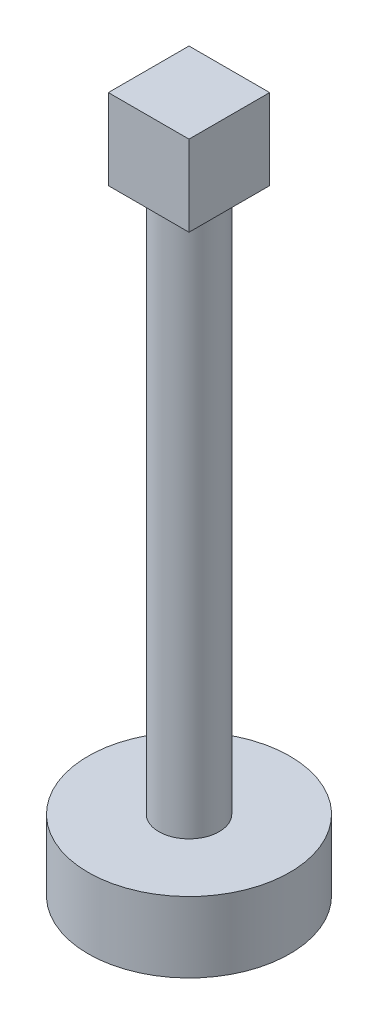
SolidWorks part; units mm, degrees
material "AISI 347 Annealed Stainless Steel (SS)"
ref_plane "Front Plane" through (0, 0, 0) normal (0, 0, 1) x (1, 0, 0)
ref_plane "Top Plane" through (0, 0, 0) normal (0, 1, 0) x (1, 0, 0)
ref_plane "Right Plane" through (0, 0, 0) normal (1, 0, 0) x (0, 0, -1)
sketch "Sketch1" plane through (0, 0, 0) normal (0, 1, 0) x (1, 0, 0)
  circle A0 centre (0, 0) radius 50
  dimension "D1" = 100
extrude "Boss-Extrude1" add sketch "Sketch1" along normal blind 35
sketch "Sketch2" plane through (0, 35, 0) normal (0, 1, 0) x (1, 0, 0)
  circle A0 centre (0, 0) radius 15
extrude "Boss-Extrude2" add sketch "Sketch2" along normal blind 270
sketch "Sketch3" plane through (0, 305, 0) normal (0, 1, 0) x (1, 0, 0)
  line L1 (-20, -20) -> (20, -20)
  line L2 (-20, -20) -> (-20, 20)
  line L3 (-20, 20) -> (20, 20)
  line L4 (20, -20) -> (20, 20)
  line L5 (-20, -20) -> (20, 20) construction
  line L6 (-20, 20) -> (20, -20) construction
  point P0 (0, 0)
  dimension "D1" = 40
  dimension "D2" = 40
extrude "Boss-Extrude3" add sketch "Sketch3" along normal blind 40
ref_point "Point1"
